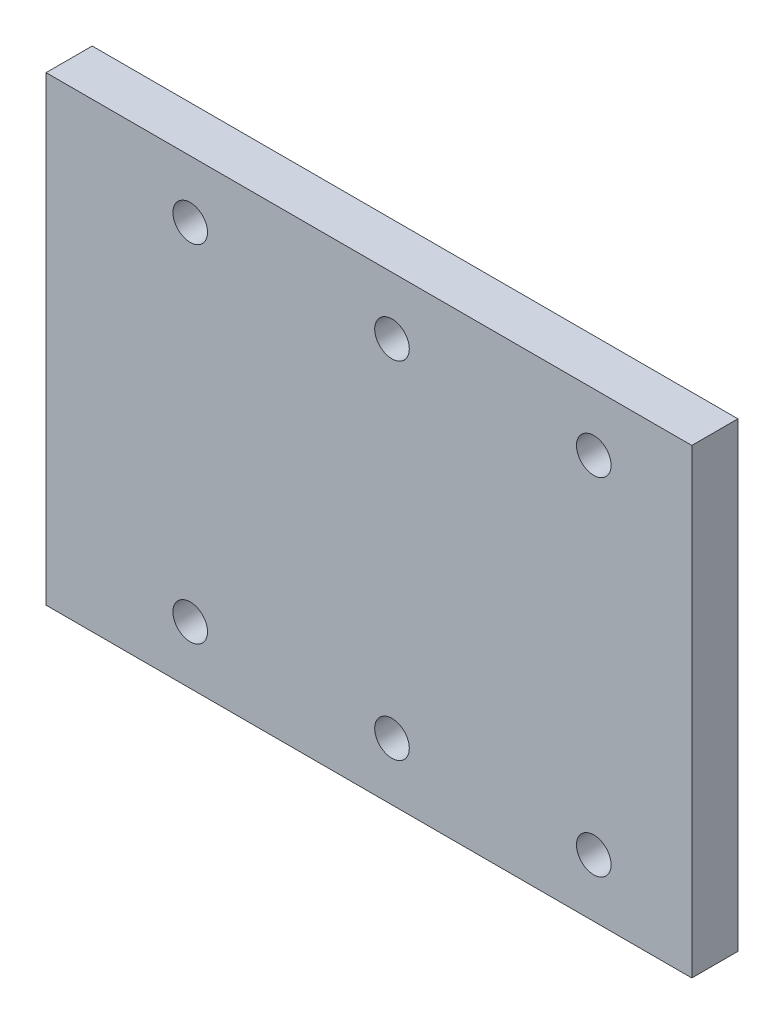
SolidWorks part; units mm, degrees
ref_plane "Plan de face" through (0, 0, 0) normal (0, 0, 1) x (1, 0, 0)
ref_plane "Plan de dessus" through (0, 0, 0) normal (0, 1, 0) x (1, 0, 0)
ref_plane "Plan de droite" through (0, 0, 0) normal (1, 0, 0) x (0, 0, -1)
sketch "Sketch1" plane through (0, 0, 0) normal (0, 0, 1) x (1, 0, 0)
  line L1 (0, 0) -> (56, 0)
  line L2 (0, 0) -> (0, 40)
  line L3 (0, 40) -> (56, 40)
  line L4 (56, 0) -> (56, 40)
  dimension "D1" = 40
  dimension "D2" = 56
extrude "Boss-Extrude1" add sketch "Sketch1" along normal blind 4
sketch "Sketch3" plane through (0, 0, 4) normal (0, 0, 1) x (1, 0, 0)
  line L0 (0, 40) -> (0, 0) construction
  line L1 (56, 0) -> (0, 0)
  line L2 (56, 0) -> (56, 3)
  line L3 (56, 3) -> (0, 3)
  line L4 (0, 0) -> (0, 3)
  dimension "D1" = 3
extrude "Cut-Extrude2" cut sketch "Sketch3" against normal blind 2
sketch "Sketch4" plane through (0, 0, 4) normal (0, 0, 1) x (1, 0, 0)
  line L0 (0, 40) -> (0, 3) construction
  line L1 (56, 40) -> (0, 40) construction
  line L2 (56, 3) -> (0, 3) construction
  circle A0 centre (47.5, 5) radius 1.5
  circle A1 centre (30, 5) radius 1.5
  circle A2 centre (12.5, 5) radius 1.5
  circle A3 centre (47.5, 35) radius 1.5
  circle A4 centre (30, 35) radius 1.5
  circle A5 centre (12.5, 35) radius 1.5
  dimension "D1" = 3
  dimension "D2" = 3
  dimension "D3" = 3
  dimension "D4" = 17.5
  dimension "D5" = 17.5
  dimension "D6" = 12.5
  dimension "D7" = 5
  dimension "D8" = 3
  dimension "D9" = 3
  dimension "D10" = 3
  dimension "D11" = 2
  dimension "D12" = 17.5
  dimension "D13" = 17.5
extrude "Cut-Extrude3" cut sketch "Sketch4" against normal through all
sketch "Sketch5" plane through (0, 0, 4) normal (0, 0, 1) x (1, 0, 0)
  line L0 (56, 3) -> (0, 3) construction
  line L1 (56, 3) -> (0, 3)
  line L2 (56, 3) -> (56, 0)
  line L3 (56, 0) -> (0, 0)
  line L4 (0, 3) -> (0, 0)
  line L5 (56, 3) -> (56, 40) construction
extrude "Boss-Extrude2" add sketch "Sketch5" against normal blind 2
